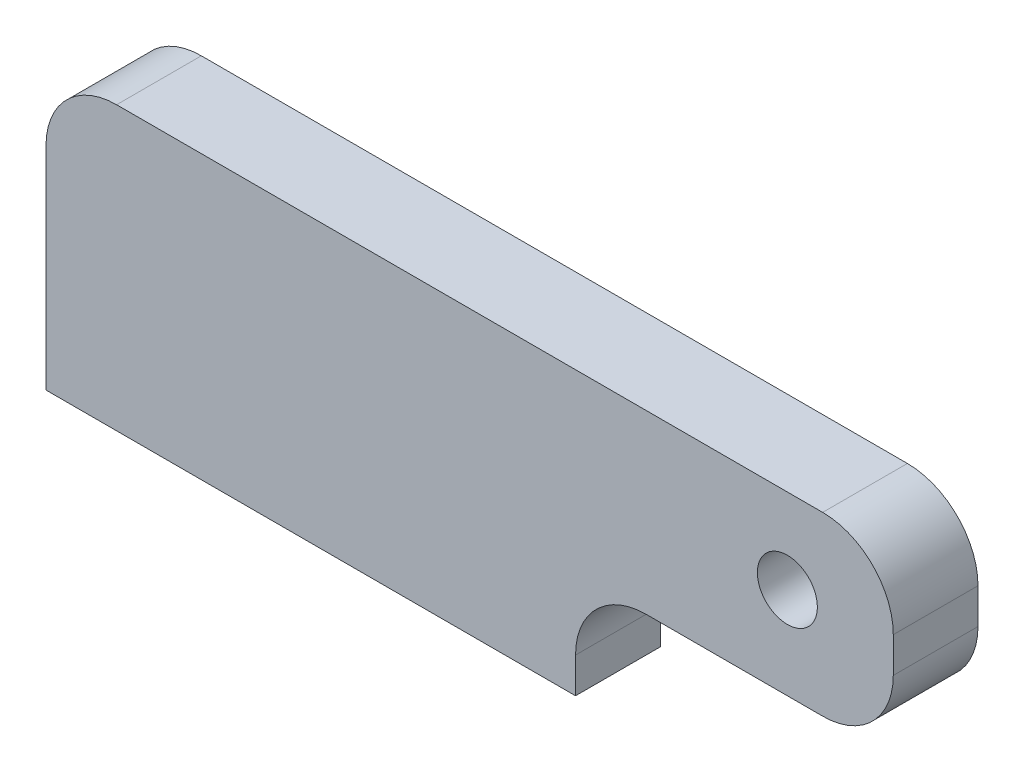
SolidWorks part; units mm, degrees
material "A3钢"
ref_plane "前视基准面" through (0, 0, 0) normal (0, 0, 1) x (1, 0, 0)
ref_plane "上视基准面" through (0, 0, 0) normal (0, 1, 0) x (1, 0, 0)
ref_plane "右视基准面" through (0, 0, 0) normal (1, 0, 0) x (0, 0, -1)
sketch "草图1" plane through (0, 0, 0) normal (0, 0, 1) x (1, 0, 0)
  line L0 (0, 0) -> (75, 0)
  line L1 (75, 0) -> (75, 15)
  line L2 (75, 15) -> (120, 15)
  line L3 (0, 0) -> (0, 40)
  line L4 (0, 40) -> (120, 40)
  line L5 (120, 40) -> (120, 15)
  dimension "D1" = 120
  dimension "D2" = 40
  dimension "D3" = 15
  dimension "D4" = 75
extrude "凸台-拉伸1" add sketch "草图1" along normal mid plane 12
hole_wizard "M6 螺纹孔1" positions "草图2" profile "草图3" tap size "M6" standard "GB"
sketch "草图2" plane through (0, 0, 0) normal (0, -1, 0) x (-1, 0, 0)
  line L0 (3.0209, 0) -> (-89.631, 0) construction
  line L3 (0, -6) -> (0, 6) construction
  point P0 (-10, 0)
  point P2 (-65, 0)
  dimension "D1" = 10
  dimension "D2" = 55
sketch "草图3" plane through (10, 0, 0) normal (1, 0, 0) x (0, 0, -1)
  line L0 (0, 0) -> (0, 19.5022)
  line L1 (0, 19.5022) -> (2.5, 18)
  line L2 (2.5, 18) -> (2.5, 0)
  line L5 (2.5, 0) -> (0, 0)
  line L10 (0, 19.5022) -> (-2.5, 18) construction
  line L11 (0, -6.35) -> (0, 107.95) construction
  dimension "螺纹孔钻头直径" = 5
  dimension "螺纹孔钻头深度" = 18
  dimension "导头角度" = 118
cosmetic thread "孔螺蚊线1" parameters "D1"=15, "D2"=6
cosmetic thread "孔螺蚊线2" parameters "D1"=15, "D2"=6
sketch "草图4" plane through (0, 0, 6) normal (0, 0, 1) x (1, 0, 0)
  line L0 (0, 0) -> (75, 0) construction
  line L1 (75, 0) -> (75, 15) construction
  circle A0 centre (105, 28) radius 5
  dimension "D2" = 10
  dimension "D1" = 28
  dimension "D3" = 30
fillet "圆角1" radius 10 4 edges at (120, 15, 0) (120, 40, 0) (0, 40, 0) (75, 15, 0)
hole_wizard "M10 螺纹孔1" positions "草图5" profile "草图6" tap size "M10" standard "GB" end condition through all
sketch "草图5" plane through (0, 0, 6) normal (0, 0, 1) x (1, 0, 0)
  point P0 (105, 28)
sketch "草图6" plane through (105, 28, 6) normal (1, 0, 0) x (0, -1, 0)
  line L0 (0, 0) -> (0, 12)
  line L1 (0, 12) -> (4.25, 12)
  line L2 (4.25, 12) -> (4.25, 0)
  line L5 (4.25, 0) -> (0, 0)
  line L11 (0, -6.35) -> (0, 107.95) construction
  dimension "通孔螺纹孔钻头直径" = 8.5
  dimension "通孔螺纹孔钻头深度" = 12
cosmetic thread "孔螺蚊线3" parameters "D2"=10
